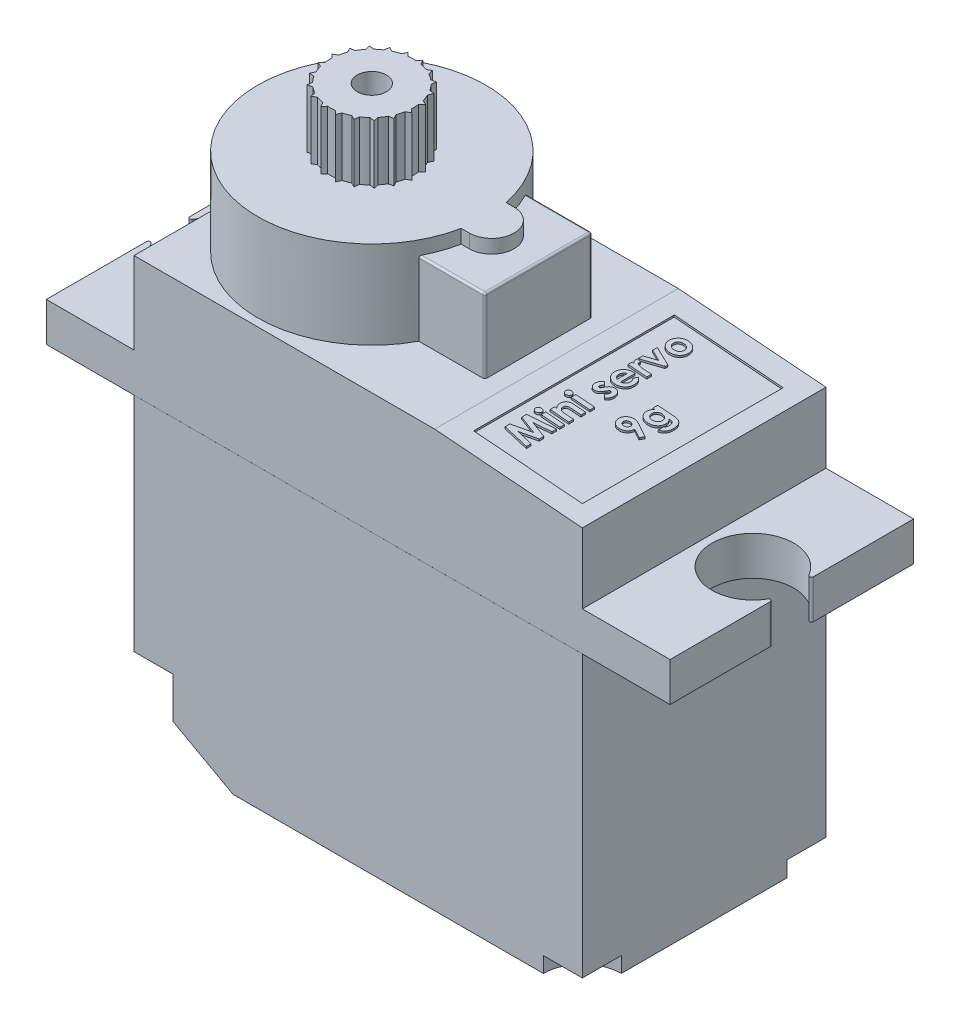
SolidWorks part; units mm, degrees
other "Camera1"
material "ABS"
ref_plane "Front Plane" through (0, 0, 0) normal (0, 0, 1) x (1, 0, 0)
ref_plane "Top Plane" through (0, 0, 0) normal (0, 1, 0) x (1, 0, 0)
ref_plane "Right Plane" through (0, 0, 0) normal (1, 0, 0) x (0, 0, -1)
sketch "Sketch1" plane through (0, 0, 0) normal (0, 1, 0) x (1, 0, 0)
  line L1 (11.5, -6.25) -> (-11.5, -6.25)
  line L2 (11.5, -6.25) -> (11.5, 6.25)
  line L3 (11.5, 6.25) -> (-11.5, 6.25)
  line L4 (-11.5, -6.25) -> (-11.5, 6.25)
  line L5 (11.5, -6.25) -> (-11.5, 6.25) construction
  line L6 (11.5, 6.25) -> (-11.5, -6.25) construction
  point P0 (0, 0)
  dimension "D1" = 12.5
  dimension "D2" = 23
extrude "Boss-Extrude1" add sketch "Sketch1" along normal blind 15.2
sketch "Sketch2" plane through (0, 15.2, 0) normal (0, 1, 0) x (1, 0, 0)
  line L1 (16, -6.249) -> (-16, -6.249)
  line L2 (16, -6.249) -> (16, 6.249)
  line L3 (16, 6.249) -> (-16, 6.249)
  line L4 (-16, -6.249) -> (-16, 6.249)
  line L5 (16, -6.249) -> (-16, 6.249) construction
  line L6 (16, 6.249) -> (-16, -6.249) construction
  point P0 (0, 0)
  dimension "D1" = 4.5
extrude "Boss-Extrude2" add sketch "Sketch2" along normal blind 2
sketch "Sketch3" plane through (0, 17.2, 0) normal (0, 1, 0) x (1, 0, 0)
  line L0 (16, 6.249) -> (-16, 6.249) construction
  line L1 (11.5, -6.249) -> (-11.5, -6.249)
  line L2 (11.5, -6.249) -> (11.5, 6.249)
  line L3 (11.5, 6.249) -> (-11.5, 6.249)
  line L4 (-11.5, -6.249) -> (-11.5, 6.249)
  line L5 (11.5, -6.249) -> (-11.5, 6.249) construction
  line L6 (11.5, 6.249) -> (-11.5, -6.249) construction
  point P0 (0, 0)
  dimension "D1" = 23
extrude "Boss-Extrude3" add sketch "Sketch3" along normal blind 4.2
sketch "Sketch4" plane through (0, 0, 6.25) normal (0, 0, 1) x (1, 0, 0)
  line L0 (11.5, 20.8) -> (3.9237, 21.4)
  line L1 (11.5, 21.4) -> (11.5, 17.2) construction
  line L2 (-11.5, 21.4) -> (11.5, 21.4) construction
  line L3 (3.9237, 21.4) -> (11.5, 21.4)
  line L4 (11.5, 21.4) -> (11.5, 20.8)
  line L5 (11.5, 17.2) -> (16, 17.2) construction
  dimension "D1" = 3.6
  dimension "D2" = 7.6
extrude "Cut-Extrude1" cut sketch "Sketch4" against normal through all
sketch "Sketch5" plane through (0, 21.4, 0) normal (0, 1, 0) x (1, 0, 0)
  line L1 (-5.55, 0) -> (-11.5, 0) construction
  line L4 (-11.5, 6.249) -> (-11.5, -6.249) construction
  line L5 (-5.55, 0) -> (0.6, 0) construction
  line L6 (0.1859, 1.15) -> (0.6, 1.15)
  line L7 (0.6, -1.15) -> (0.1859, -1.15)
  arc A1 (0.6, 1.15) -> (0.6, -1.15) centre (0.6, 0) cw
  arc A2 (0.1859, 1.15) -> (0.1859, -1.15) centre (-5.55, 0) ccw
  dimension "D1" = 5.85
  dimension "D4" = 1.15
  dimension "D2" = 5.95
  dimension "D3" = 6.15
extrude "Boss-Extrude4" add sketch "Sketch5" along normal blind 4.5
sketch "Sketch6" plane through (0, 21.4, 0) normal (0, 1, 0) x (1, 0, 0)
  line L1 (-1.8, -2.75) -> (3, -2.75)
  line L2 (-1.8, -2.75) -> (-1.8, 2.75)
  line L3 (-1.8, 2.75) -> (3, 2.75)
  line L4 (3, -2.75) -> (3, 2.75)
  line L5 (-1.8, -2.75) -> (3, 2.75) construction
  line L6 (-1.8, 2.75) -> (3, -2.75) construction
  arc A1 (0.6, -1.15) -> (0.6, 1.15) centre (0.6, 0) ccw construction
  arc A2 (0.1859, 1.15) -> (0.1859, -1.15) centre (-5.55, 0) ccw construction
  point P0 (0.6, 0)
  dimension "D1" = 8.55
  dimension "D2" = 5.5
extrude "Boss-Extrude5" add sketch "Sketch6" along normal blind 3.8
sketch "Sketch8" plane through (0, 25.9, 0) normal (0, 1, 0) x (1, 0, 0)
  circle A0 centre (-5.55, 0) radius 2.35
  arc A1 (0.1859, 1.15) -> (0.1859, -1.15) centre (-5.55, 0) ccw construction
  circle A2 centre (-5.55, 0) radius 0.75
  dimension "D1" = 4.7
  dimension "D2" = 1.5
extrude "Boss-Extrude8" add sketch "Sketch8" along normal blind 3 separate body
sketch "Sketch9" plane through (0, 0, 6.25) normal (0, 0, 1) x (1, 0, 0)
  line L0 (-11.5, 0) -> (-6.4206, 0)
  line L1 (-11.5, 0) -> (11.5, 0) construction
  line L2 (-6.4206, 0) -> (-11.5, 2.8)
  line L3 (-11.5, 15.2) -> (-11.5, 0) construction
  line L4 (-11.5, 2.8) -> (-11.5, 0)
  dimension "D1" = 5.8
  dimension "D2" = 2.8
extrude "Cut-Extrude2" cut sketch "Sketch9" against normal through all
sketch "Sketch12" plane through (0, 17.2, 0) normal (0, 1, 0) x (1, 0, 0)
  line L5 (16, -6.249) -> (16, 6.249) construction
  line L6 (16, 0) -> (14, 0) construction
  circle A0 centre (14, 0) radius 2.1
  dimension "D1" = 4.2
  dimension "D2" = 14
sketch "Sketch14" plane through (0, 28.9, 0) normal (0, 1, 0) x (1, 0, 0)
  line L0 (-7.8562, -0.4516) -> (-7.6828, -0.2715)
  line L1 (-7.6969, 0.1161) -> (-7.8829, 0.2831)
  line L2 (-7.8829, 0.2831) -> (-5.55, 0) construction
  line L3 (-5.55, 0) -> (-7.8562, -0.4516) construction
  line L4 (-5.55, 0) -> (-8.018, -0.0896) construction
  line L5 (-7.8829, 0.2831) -> (-7.4891, -0.0704) construction
  line L6 (-7.4891, -0.0704) -> (-7.8562, -0.4516) construction
  circle A1 centre (-5.55, 0) radius 2.35 construction
  arc A2 (-7.6828, -0.2715) -> (-7.6969, 0.1161) centre (-5.55, 0) cw
  arc A3 (-7.8829, 0.2831) -> (-7.8562, -0.4516) centre (-7.4891, -0.0704) ccw
  dimension "D1" = 2.15
  dimension "D2" = 35
  dimension "D3" = 18
extrude "Enlèv. mat.-Extru.1" cut sketch "Sketch14" against normal up to next (3 mm away)
pattern_circular "Répétition circulaire2" count 20 every 18 about axis through (-5.55, 0, 0) along (0, 1, 0) of "Enlèv. mat.-Extru.1"
extrude "Cut-Extrude11" cut sketch "Sketch12" against normal blind 10
mirror "Mirror1" about plane through (0, 0, 0) normal (1, 0, 0) of "Cut-Extrude11"
sketch "Sketch15" plane through (0, 0, 0) normal (0, -1, 0) x (1, 0, 0)
  line L0 (11.5, 6.25) -> (11.5, -6.25) construction
  line L1 (-6.4206, 6.25) -> (11.5, 6.25) construction
  line L2 (9.5, 6.25) -> (11.5, 6.25)
  line L3 (11.5, 6.25) -> (11.5, 4.25)
  line L4 (4.5258, 0) -> (-4.7559, 0) construction
  line L5 (11.5, -6.25) -> (11.5, -4.25)
  line L6 (9.5, -6.25) -> (11.5, -6.25)
  arc A0 (11.5, 4.25) -> (9.5, 6.25) centre (11.5, 6.25) cw
  arc A1 (11.5, -4.25) -> (9.5, -6.25) centre (11.5, -6.25) ccw
  dimension "D1" = 2
extrude "Cut-Extrude12" cut sketch "Sketch15" against normal blind 0.8
sketch "Sketch16" plane through (0, 0, 0) normal (0, -1, 0) x (1, 0, 0)
  line L0 (-6.4206, 6.25) -> (-11.5, 6.25) construction
  line L1 (-11.5, -6.25) -> (-11.5, 6.25) construction
  line L2 (-11.5, -6.249) -> (-11.5, 6.249) construction
  line L3 (-11.5, 4.25) -> (-11.5, 6.25)
  line L4 (-11.5, 6.25) -> (-9.5, 6.25)
  line L5 (-1.3995, 0) -> (2.6342, 0) construction
  line L6 (-11.5, -6.25) -> (-9.5, -6.25)
  line L7 (-11.5, -4.25) -> (-11.5, -6.25)
  arc A0 (-9.5, 6.25) -> (-11.5, 4.25) centre (-11.5, 6.25) cw
  arc A1 (-9.5, -6.25) -> (-11.5, -4.25) centre (-11.5, -6.25) ccw
  dimension "D1" = 2
extrude "Cut-Extrude13" cut sketch "Sketch16" against normal blind 3.8
sketch "Sketch17" plane through (1.7087, 21.5754, 0) normal (0.0789, 0.9969, 0) x (0.9969, -0.0789, 0)
  line L1 (8.822, -5.25) -> (3.222, -5.25)
  line L2 (8.822, -5.25) -> (8.822, 5.05)
  line L3 (8.822, 5.05) -> (3.222, 5.05)
  line L4 (3.222, -5.25) -> (3.222, 5.05)
  line L8 (2.222, 6.249) -> (2.222, -6.249) construction
  line L9 (9.822, 6.249) -> (9.822, -6.249) construction
  line L10 (2.222, -6.25) -> (9.822, -6.25) construction
  dimension "D1" = 1
  dimension "D2" = 1
  dimension "D3" = 1
  dimension "D4" = 10.3
extrude "Cut-Extrude14" cut sketch "Sketch17" against normal blind 0.1
sketch "Sketch19" plane through (1.7008, 21.4757, 0) normal (0.0789, 0.9969, 0) x (0.9969, -0.0789, 0)
  line L0 (5.1279, -5.25) -> (5.1279, 5.05) construction
  line L4 (3.222, -5.25) -> (8.822, -5.25) construction
  line L5 (8.822, 5.05) -> (3.222, 5.05) construction
  line L6 (7.5214, 5.05) -> (7.5214, -5.25) construction
  text T0 "<b>Mini servo</b>" font "Century Gothic" height in points 5
  text T1 "<b>9g</b>" font "Century Gothic" height in points 5
extrude "Boss-Extrude9" add sketch "Sketch19" along normal up to surface (0.1 mm away) up to face at (7.7119, 21.1, 0.1)
fillet "Fillet3" radius 0.1 9 edges at (3, 25.2, 0) (1.3067, 25.2, 2.75) (3, 23.3, 2.75) (3, 23.3, -2.75) (1.3067, 25.2, -2.75) (16, 16.2, -0.6403) (16, 16.2, 0.6403) (-16, 16.2, -0.6403) (-16, 16.2, 0.6403)
